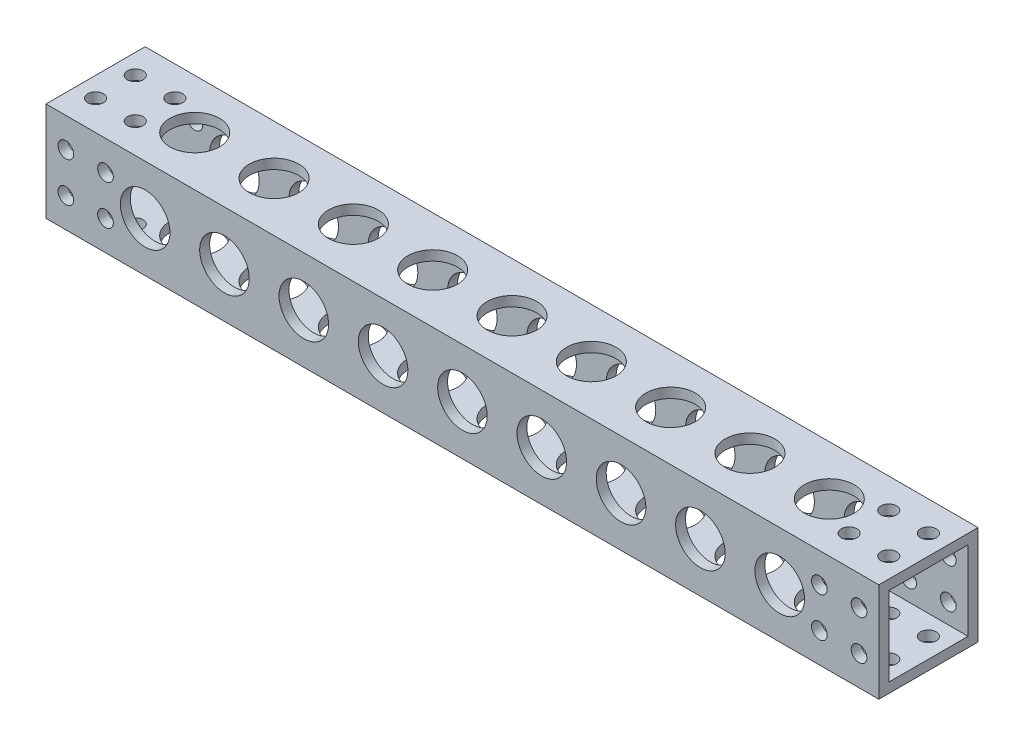
SolidWorks part; units mm, degrees
material "6061-T6 (SS)"
ref_plane "Front Plane" through (0, 0, 0) normal (0, 0, 1) x (1, 0, 0)
ref_plane "Top Plane" through (0, 0, 0) normal (0, 1, 0) x (1, 0, 0)
ref_plane "Right Plane" through (0, 0, 0) normal (1, 0, 0) x (0, 0, -1)
sketch "Sketch1" plane through (0, 0, 0) normal (0, 0, 1) x (1, 0, 0)
  line L1 (0, 0) -> (-266.7, 0)
  line L2 (0, 0) -> (0, -31.75)
  line L3 (0, -31.75) -> (-266.7, -31.75)
  line L4 (-266.7, 0) -> (-266.7, -31.75)
  dimension "D1" = 266.7
  dimension "D2" = 31.75
extrude "Boss-Extrude1" add sketch "Sketch1" along normal blind 31.75
sketch "Sketch2" plane through (0, 0, 31.75) normal (0, 0, 1) x (1, 0, 0)
  line L0 (-266.7, -31.75) -> (0, -31.75) construction
  line L1 (-266.7, 0) -> (-266.7, -31.75) construction
  circle A0 centre (-234.95, -15.875) radius 7.9375
  dimension "D1" = 15.875
  dimension "D3" = 15.875
  dimension "D2" = 31.75
extrude "Cut-Extrude1" cut sketch "Sketch2" against normal blind 31.75
pattern_linear "LPattern1" count 9 spacing 25.4 along (1, 0, 0) of "Cut-Extrude1"
sketch "Sketch3" plane through (0, 0, 31.75) normal (0, 0, 1) x (1, 0, 0)
  line L0 (-266.7, -31.75) -> (0, -31.75) construction
  line L1 (-266.7, 0) -> (-266.7, -31.75) construction
  circle A0 centre (-260.35, -9.525) radius 2.5082
  circle A1 centre (-247.65, -9.525) radius 2.5082
  circle A2 centre (-260.35, -22.225) radius 2.5082
  circle A3 centre (-247.65, -22.225) radius 2.5082
  point P8 (-254, -15.875)
  dimension "D1" = 5.0165
  dimension "D2" = 15.875
  dimension "D3" = 12.7
  dimension "D4" = 6.35
  dimension "D5" = 6.35
  dimension "D6" = 6.35
  dimension "D7" = 6.35
  dimension "D8" = 6.35
  dimension "D9" = 6.35
  dimension "D10" = 6.35
  dimension "D11" = 6.35
extrude "Cut-Extrude2" cut sketch "Sketch3" against normal blind 31.75
sketch "Sketch4" plane through (0, 0, 0) normal (1, 0, 0) x (0, 0, -1)
  line L0 (-31.75, -31.75) -> (-31.75, 0) construction
  line L1 (-28.575, -3.175) -> (-3.175, -3.175)
  line L2 (-28.575, -3.175) -> (-28.575, -28.575)
  line L3 (-28.575, -28.575) -> (-3.175, -28.575)
  line L4 (-3.175, -3.175) -> (-3.175, -28.575)
  line L5 (-31.75, -31.75) -> (0, -31.75) construction
  dimension "D1" = 25.4
  dimension "D2" = 25.4
  dimension "D3" = 3.175
  dimension "D4" = 3.175
extrude "Cut-Extrude3" cut sketch "Sketch4" against normal blind 266.7
ref_plane "Plane1" through (-133.35, 0, 0) normal (1, 0, 0) x (0, 0, -1)
mirror "Mirror1" about plane through (-133.35, 0, 0) normal (1, 0, 0) of "Cut-Extrude2"
ref_plane "Plane2" through (0, -15.875, 0) normal (0, 1, 0) x (1, 0, 0)
sketch "Sketch5" plane through (0, 0, 0) normal (0, 1, 0) x (1, 0, 0)
  line L0 (0, -31.75) -> (0, 0) construction
  line L1 (0, -31.75) -> (-266.7, -31.75) construction
  circle A0 centre (-31.75, -15.875) radius 7.9375
  dimension "D1" = 15.875
  dimension "D2" = 31.75
  dimension "D3" = 15.875
extrude "Cut-Extrude4" cut sketch "Sketch5" against normal blind 31.75
pattern_linear "LPattern2" count 9 spacing 25.4 along (-1, 0, 0) of "Cut-Extrude4"
sketch "Sketch6" plane through (0, 0, 0) normal (0, 1, 0) x (1, 0, 0)
  line L0 (0, -31.75) -> (-266.7, -31.75) construction
  line L1 (0, -31.75) -> (0, 0) construction
  circle A0 centre (-19.05, -9.525) radius 2.5082
  circle A1 centre (-6.35, -9.525) radius 2.5083
  circle A2 centre (-19.05, -22.225) radius 2.5082
  circle A3 centre (-6.35, -22.225) radius 2.5082
  point P8 (-12.7, -15.875)
  dimension "D1" = 15.875
  dimension "D3" = 5.0165
  dimension "D2" = 12.7
  dimension "D4" = 6.35
  dimension "D5" = 6.35
  dimension "D6" = 6.35
  dimension "D7" = 6.35
  dimension "D8" = 6.35
  dimension "D9" = 6.35
  dimension "D10" = 6.35
  dimension "D11" = 6.35
extrude "Cut-Extrude5" cut sketch "Sketch6" against normal blind 31.75
mirror "Mirror2" about plane through (-133.35, 0, 0) normal (1, 0, 0) of "Cut-Extrude5"
